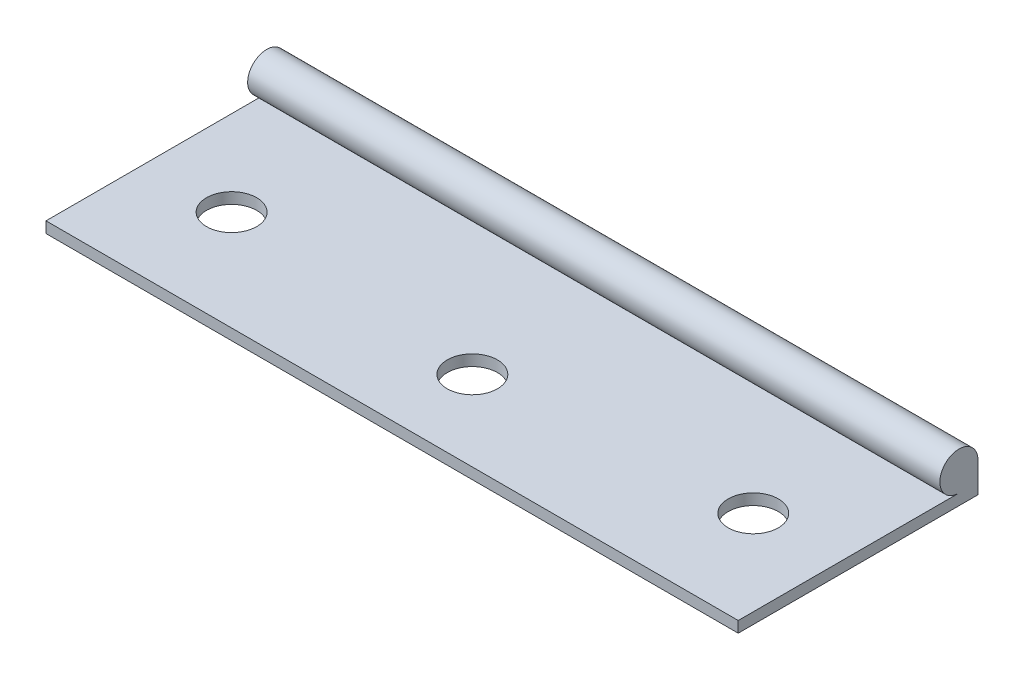
SolidWorks part; units mm, degrees
material "AISI 304"
ref_plane "Front" through (0, 0, 0) normal (0, 0, 1) x (1, 0, 0)
ref_plane "Top" through (0, 0, 0) normal (0, 1, 0) x (1, 0, 0)
ref_plane "Right" through (0, 0, 0) normal (1, 0, 0) x (0, 0, -1)
sketch "草图1" plane through (0, 0, 0) normal (1, 0, 0) x (0, 0, -1)
  line L0 (0, 0) -> (0, 1.1)
  line L1 (0, 1.1) -> (19, 1.1)
  line L2 (0, 0) -> (19, 0)
  line L3 (19, 0) -> (19, 10.8121) construction
  line L4 (19, 1.1) -> (22, 1.1)
  line L5 (19, 0) -> (23.9, 0)
  line L6 (23.9, 0) -> (23.9, 3)
  circle A0 centre (22, 3) radius 3 construction
  circle A1 centre (22, 3) radius 1.9
  dimension "D3" = 6
  dimension "D1" = 1.1
  dimension "D2" = 19
extrude "凸台-拉伸1" add sketch "草图1" along normal blind 69 contours A1 | A1 L4 L1 L0 L2 L5 L6
sketch "草图2" plane through (0, 1.1, 0) normal (0, 1, 0) x (1, 0, 0)
  line L0 (0, 10) -> (69, 10) construction
  line L1 (0, 0) -> (0, 22) construction
  line L2 (69, 0) -> (69, 22) construction
  line L3 (69, 0) -> (0, 0) construction
  line L4 (34.5, 10) -> (34.5, -0.9364) construction
  line L5 (69, 0) -> (0, 0) construction
  circle A0 centre (8.5, 10) radius 2.5
  circle A1 centre (60.5, 10) radius 2.5
  circle A2 centre (34.5, 8) radius 2.5
  dimension "D1" = 5
  dimension "D2" = 5
  dimension "D6" = 8
  dimension "D3" = 8.5
  dimension "D4" = 10
  dimension "D5" = 8.5
extrude "切除-拉伸1" cut sketch "草图2" against normal through all
